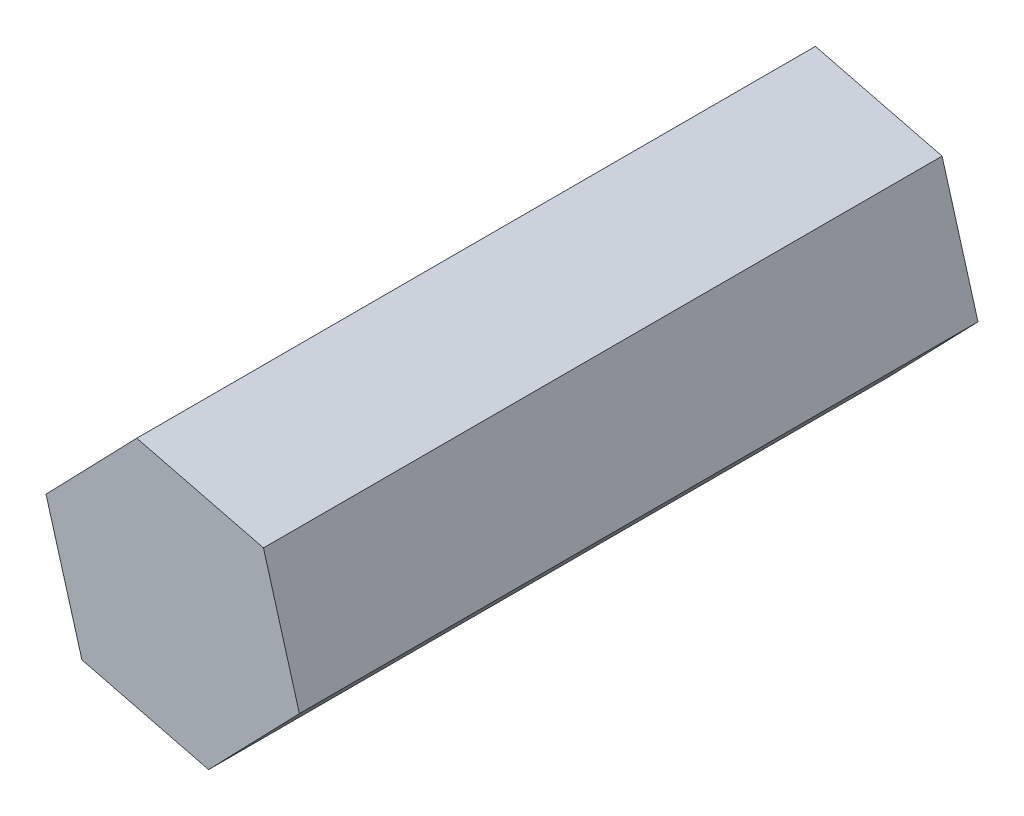
SolidWorks part; units mm, degrees
ref_plane "Front Plane" through (0, 0, 0) normal (0, 0, 1) x (1, 0, 0)
ref_plane "Top Plane" through (0, 0, 0) normal (0, 1, 0) x (1, 0, 0)
ref_plane "Right Plane" through (0, 0, 0) normal (1, 0, 0) x (0, 0, -1)
sketch "Sketch1" plane through (0, 0, 0) normal (0, 0, 1) x (1, 0, 0)
  line L1 (-7.1134, 1.7784) -> (-5.0968, -5.2712)
  line L2 (-5.0968, -5.2712) -> (2.0166, -7.0496)
  line L3 (2.0166, -7.0496) -> (7.1134, -1.7784)
  line L4 (7.1134, -1.7784) -> (5.0968, 5.2712)
  line L5 (5.0968, 5.2712) -> (-2.0166, 7.0496)
  line L6 (-2.0166, 7.0496) -> (-7.1134, 1.7784)
  circle A0 centre (0, 0) radius 6.35 construction
  dimension "D1" = 12.7
extrude "Boss-Extrude1" add sketch "Sketch1" along normal blind 38.1
sketch "Sketch2" plane through (0, 0, 0) normal (0, 0, -1) x (-1, 0, 0)
  circle A0 centre (0, 0) radius 1.822
extrude "Cut-Extrude1" cut sketch "Sketch2" against normal blind 2.54
